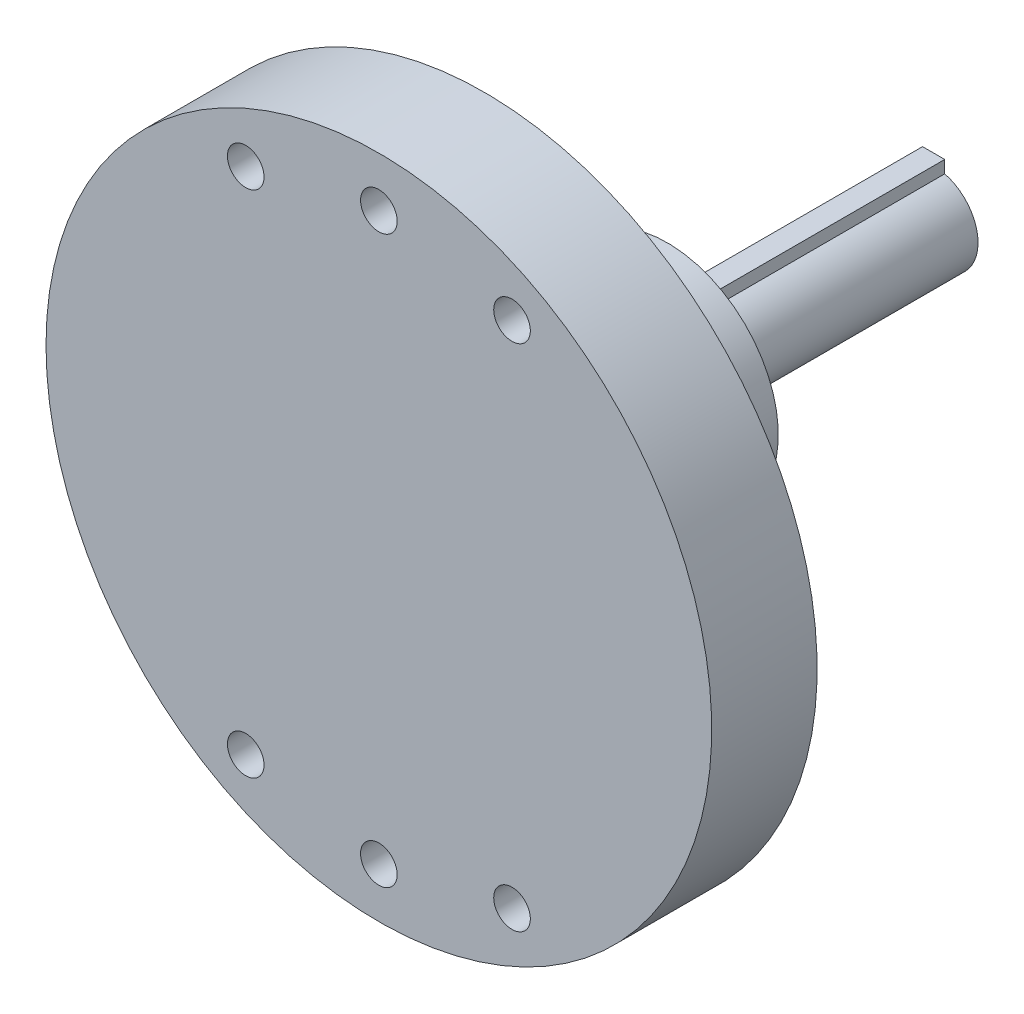
SolidWorks part; units mm, degrees
ref_plane "Front Plane" through (0, 0, 0) normal (0, 0, 1) x (1, 0, 0)
ref_plane "Top Plane" through (0, 0, 0) normal (0, 1, 0) x (1, 0, 0)
ref_plane "Right Plane" through (0, 0, 0) normal (1, 0, 0) x (0, 0, -1)
ref_plane "Plane1" through (0, 0, 0) normal (0, -1, 0) x (1, 0, 0)
sketch "Sketch1" plane through (0, 0, 0) normal (0, -1, 0) x (1, 0, 0)
  line L0 (30, 10) -> (0, 10)
  line L1 (0, 10) -> (0, 0.5)
  line L2 (0, 0.5) -> (30, 0.5)
  line L3 (30, 0.5) -> (30, 10)
  line L4 (0, 10) -> (0, 0.5) construction
revolve "Revolve1" add sketch "Sketch1" angle 360 about L4
sketch "Sketch2" plane through (0, 0, 0.5) normal (0, 0, -1) x (-1, 0, 0)
  arc A0 (1.9019, -26.9329) -> (10.5623, -24.8483) centre (0, 0) ccw
  arc A1 (10.5623, -24.8483) -> (14.3793, -22.8525) centre (12, -22.95) ccw
  arc A2 (14.3793, -22.8525) -> (14.3793, 22.8525) centre (0, 0) ccw
  arc A3 (14.3793, 22.8525) -> (10.5623, 24.8483) centre (12, 22.95) ccw
  arc A4 (10.5623, 24.8483) -> (1.9019, 26.9329) centre (0, 0) ccw
  arc A5 (1.9019, 26.9329) -> (-1.9019, 26.9329) centre (0, 25.5) ccw
  arc A6 (-1.9019, 26.9329) -> (-10.5623, 24.8483) centre (0, 0) ccw
  arc A7 (-10.5623, 24.8483) -> (-14.3793, 22.8525) centre (-12, 22.95) ccw
  arc A8 (-14.3793, 22.8525) -> (-14.3793, -22.8525) centre (0, 0) ccw
  arc A9 (-14.3793, -22.8525) -> (-10.5623, -24.8483) centre (-12, -22.95) ccw
  arc A10 (-10.5623, -24.8483) -> (-1.9019, -26.9329) centre (0, 0) ccw
  arc A11 (-1.9019, -26.9329) -> (1.9019, -26.9329) centre (0, -25.5) ccw
extrude "Cut-Extrude1" cut sketch "Sketch2" against normal blind 3.5
sketch "Sketch3" plane through (0, 0, 4) normal (0, 0, -1) x (-1, 0, 0)
  circle A0 centre (0, 0) radius 17.4
extrude "Boss-Extrude1" add sketch "Sketch3" along normal blind 4
sketch "Sketch4" plane through (0, 0, 0) normal (0, 0, -1) x (-1, 0, 0)
  circle A0 centre (0, 0) radius 10
extrude "Boss-Extrude2" add sketch "Sketch4" along normal blind 16
sketch "Sketch5" plane through (0, 0, 10) normal (0, 0, 1) x (1, 0, 0)
  line L0 (1, 5) -> (-1, 5)
  line L1 (-1, 5) -> (-1, 3.873)
  line L2 (1, 3.873) -> (1, 5)
  arc A0 (-1, 3.873) -> (1, 3.873) centre (0, 0) cw
extrude "Cut-Extrude2" cut sketch "Sketch5" against normal through all
sketch "Sketch6" plane through (0, 0, 0) normal (0, -1, 0) x (1, 0, 0)
  line L0 (4, 10) -> (0, 10)
  line L1 (0, 10) -> (0, -16)
  line L2 (0, -16) -> (4, -16)
  line L3 (4, -16) -> (4, 10)
  line L4 (0, 10) -> (0, -16) construction
revolve "Cut-Revolve1" cut sketch "Sketch6" angle 360 about L4
hole_wizard "#4 Clearance Hole1" positions "Sketch8" profile "Sketch7" hole size "#4" standard "ANSI Inch"
sketch "Sketch8" plane through (0, 0, 4) normal (0, 0, -1) x (-1, 0, 0)
  point P0 (12, -22.95)
  point P1 (0, -25.5)
  point P2 (-12, -22.95)
  point P3 (-12, 22.95)
  point P4 (0, 25.5)
  point P5 (12, 22.95)
sketch "Sketch7" plane through (-12, -22.95, 4) normal (1, 0, 0) x (0, 1, 0)
  line L0 (0, 0) -> (0, 6)
  line L1 (0, 6) -> (1.65, 6)
  line L2 (1.65, 6) -> (1.65, 0)
  line L5 (1.65, 0) -> (0, 0)
  line L11 (0, -6.35) -> (0, 107.95) construction
  dimension "Thru Hole Dia." = 3.3
  dimension "Thru Hole Depth" = 6
hole_wizard "#2 Clearance Hole1" positions "Sketch10" profile "Sketch9" hole size "#2" standard "ANSI Inch"
sketch "Sketch10" plane through (0, 0, -16) normal (0, 0, -1) x (-1, 0, 0)
  point P0 (-5.0558, -5.0558)
  point P1 (5.0558, -5.0558)
  point P2 (5.0558, 5.0558)
  point P3 (-5.0558, 5.0558)
sketch "Sketch9" plane through (5.0558, -5.0558, -16) normal (1, 0, 0) x (0, 1, 0)
  line L0 (0, 0) -> (0, 12)
  line L1 (0, 12) -> (1.25, 12)
  line L2 (1.25, 12) -> (1.25, 0)
  line L5 (1.25, 0) -> (0, 0)
  line L10 (0, 12) -> (-1.25, 12) construction
  line L11 (0, -6.35) -> (0, 107.95) construction
  dimension "Hole Dia." = 2.5
  dimension "Hole Depth" = 12
  dimension "Drill Angle" = 180
hole_wizard "#2 Clearance Hole2" positions "3DSketch1" profile "Sketch11" hole size "#2" standard "ANSI Inch"
sketch3d "3DSketch1"
  point P0 (0, -10, -6.2763)
sketch "Sketch11" plane through (0, -10, -6.2763) normal (1, 0, 0) x (0, 0, -1)
  line L0 (0, 0) -> (0, 6)
  line L1 (0, 6) -> (1.25, 6)
  line L2 (1.25, 6) -> (1.25, 0)
  line L5 (1.25, 0) -> (0, 0)
  line L11 (0, -6.35) -> (0, 107.95) construction
  dimension "Thru Hole Dia." = 2.5
  dimension "Thru Hole Depth" = 6
hole_wizard "#2 Clearance Hole3" positions "3DSketch2" profile "Sketch12" hole size "#2" standard "ANSI Inch"
sketch3d "3DSketch2"
  point P0 (0, 10, -6.2763)
sketch "Sketch12" plane through (0, 10, -6.2763) normal (1, 0, 0) x (0, 0, 1)
  line L0 (0, 0) -> (0, 40)
  line L1 (0, 40) -> (1.25, 40)
  line L2 (1.25, 40) -> (1.25, 0)
  line L5 (1.25, 0) -> (0, 0)
  line L11 (0, -6.35) -> (0, 107.95) construction
  dimension "Thru Hole Dia." = 2.5
  dimension "Thru Hole Depth" = 40
fillet "Fillet1" radius 3 1 edges at (-10, 0, 0)
sketch "草图1" plane through (0, 0, 10) normal (0, 0, 1) x (1, 0, 0)
  line L0 (-1, 5) -> (-1, 3.873) construction
  line L1 (1, 5) -> (-1, 5) construction
  line L2 (1, 3.873) -> (1, 5) construction
  line L3 (-1, 5) -> (-1, 3.873)
  line L4 (1, 5) -> (-1, 5)
  line L5 (1, 3.873) -> (1, 5)
  arc A0 (-1, 3.873) -> (1, 3.873) centre (0, 0) ccw construction
  arc A1 (-1, 3.873) -> (1, 3.873) centre (0, 0) ccw
extrude "凸台-拉伸1" add sketch "草图1" against normal blind 50
